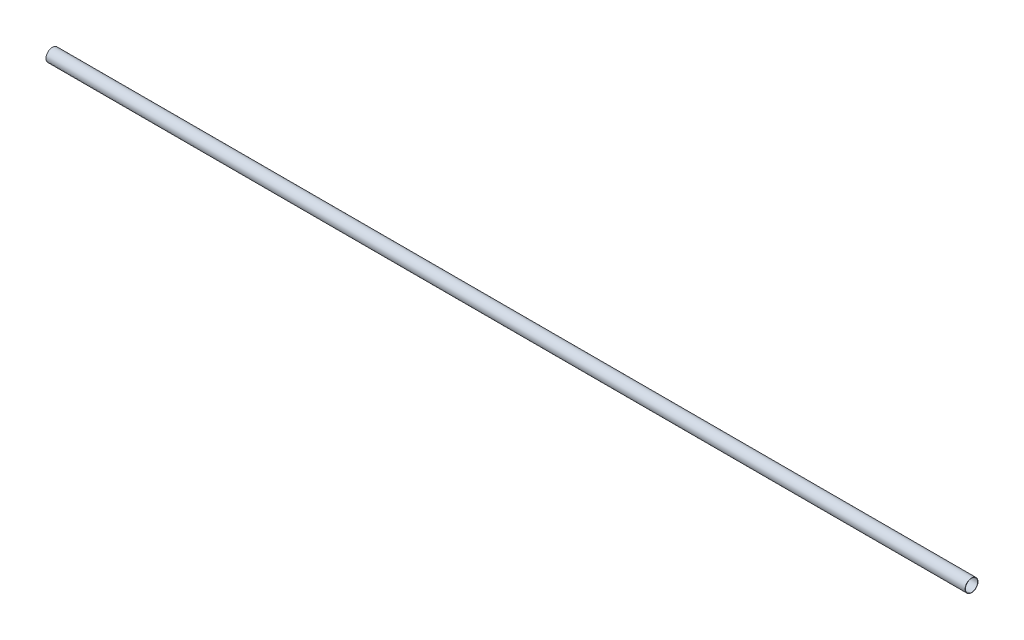
SolidWorks part; units mm, degrees
ref_plane "Front Plane" through (0, 0, 0) normal (0, 0, 1) x (1, 0, 0)
ref_plane "Top Plane" through (0, 0, 0) normal (0, 1, 0) x (1, 0, 0)
ref_plane "Right Plane" through (0, 0, 0) normal (1, 0, 0) x (0, 0, -1)
sketch "Sketch1" plane through (0, 0, 0) normal (1, 0, 0) x (0, 0, -1)
  circle A0 centre (0, 0) radius 2
  dimension "D1" = 4
extrude "Extrude-Thin1" add sketch "Sketch1" along normal blind 300 thin
